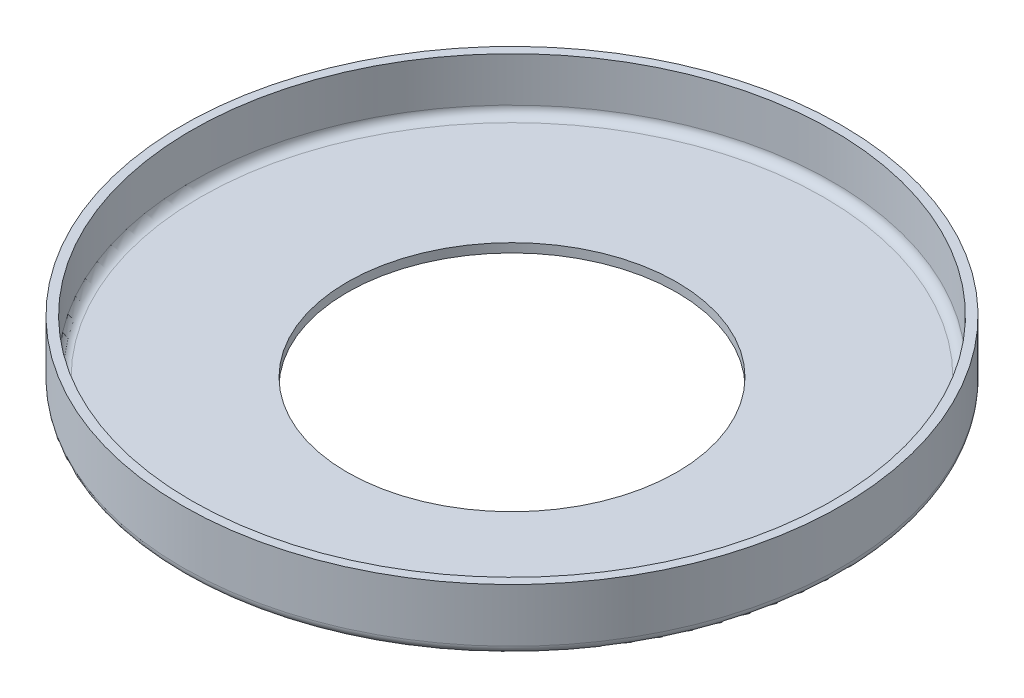
SolidWorks part; units mm, degrees
material "1060 Alloy"
ref_plane "Front Plane" through (0, 0, 0) normal (0, 0, 1) x (1, 0, 0)
ref_plane "Top Plane" through (0, 0, 0) normal (0, 1, 0) x (1, 0, 0)
ref_plane "Right Plane" through (0, 0, 0) normal (1, 0, 0) x (0, 0, -1)
sketch "Sketch1" plane through (0, 0, 0) normal (0, 1, 0) x (1, 0, 0)
  circle A0 centre (0, 0) radius 37
  dimension "D1" = 74
extrude "Boss-Extrude1" add sketch "Sketch1" along normal blind 7
sketch "Sketch2" plane through (0, 7, 0) normal (0, 1, 0) x (1, 0, 0)
  circle A0 centre (0, 0) radius 36
  dimension "D1" = 72
extrude "Cut-Extrude1" cut sketch "Sketch2" against normal blind 6
sketch "Sketch3" plane through (0, 1, 0) normal (0, 1, 0) x (1, 0, 0)
  circle A0 centre (0, 0) radius 18.5
  dimension "D1" = 37
extrude "Cut-Extrude2" cut sketch "Sketch3" against normal blind 6
fillet "Fillet1" radius 1 2 edges at (0, 0, 37) (0, 1, 36)
